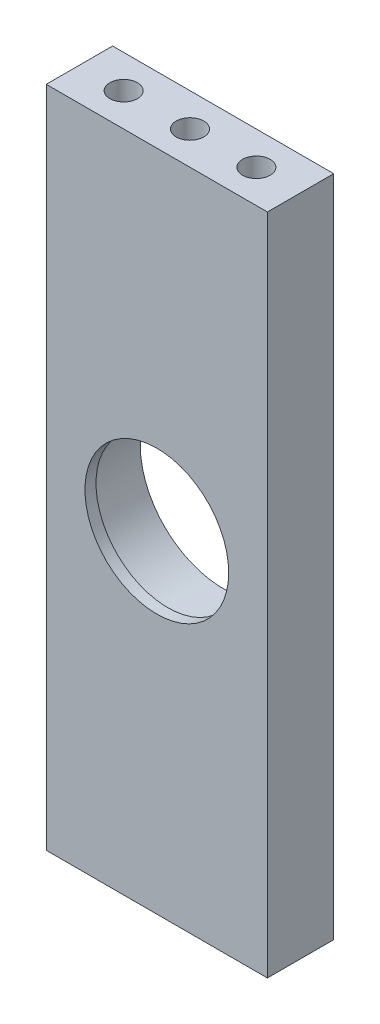
SolidWorks part; units mm, degrees
ref_plane "정면" through (0, 0, 0) normal (0, 0, 1) x (1, 0, 0)
ref_plane "윗면" through (0, 0, 0) normal (0, 1, 0) x (1, 0, 0)
ref_plane "우측면" through (0, 0, 0) normal (1, 0, 0) x (0, 0, -1)
sketch "스케치1" plane through (0, 0, 0) normal (0, 0, 1) x (1, 0, 0)
  line L2 (-7.7841, 20.7102) -> (-7.7841, -9.2898)
  line L3 (-7.7841, -9.2898) -> (12.2159, -9.2898)
  line L4 (12.2159, 20.7102) -> (12.2159, -9.2898)
  line L6 (-7.7841, 20.7102) -> (-7.7841, 50.7102)
  line L7 (-7.7841, 50.7102) -> (12.2159, 50.7102)
  line L8 (12.2159, 20.7102) -> (12.2159, 50.7102)
  circle A0 centre (2.2159, 20.7102) radius 7.5
  dimension "D3" = 15
  dimension "D1" = 20
  dimension "D2" = 30
extrude "보스-돌출1" add sketch "스케치1" along normal blind 6
sketch "스케치2" plane through (0, 0, 6) normal (0, 0, 1) x (1, 0, 0)
  circle A1 centre (2.2159, 20.7102) radius 6.5
  circle A2 centre (2.2159, 20.7102) radius 7.5
  circle A3 centre (2.2159, 20.7102) radius 7.5
  dimension "D1" = 0
  dimension "D2" = 1
extrude "보스-돌출3" add sketch "스케치2" against normal blind 1
sketch "스케치3" plane through (0, -9.2898, 0) normal (0, -1, 0) x (1, 0, 0)
  line L0 (-7.7841, 3) -> (49992.2159, 3) construction
  line L2 (-7.7841, 0) -> (12.2159, 0) construction
  line L3 (2.2159, 4) -> (2.2159, -49996) construction
  line L4 (-7.7841, 6) -> (12.2159, 6) construction
  circle A0 centre (2.2159, 3) radius 1.5
  circle A1 centre (-3.7841, 3) radius 1.5
  circle A2 centre (8.2159, 3) radius 1.5
  point P8 (2.2159, 6)
  dimension "D2" = 3
  dimension "D3" = 3
  dimension "D4" = 3
  dimension "D1" = 3
  dimension "D5" = 6
  dimension "D6" = 6
sketch "스케치4" plane through (0, 50.7102, 0) normal (0, 1, 0) x (1, 0, 0)
  line L0 (-7.7841, -3) -> (49992.2159, -3) construction
  line L1 (-7.7841, -6) -> (-7.7841, 0) construction
  line L2 (2.2159, -2) -> (2.2159, 49998) construction
  circle A0 centre (8.2159, -3) radius 1.5
  circle A1 centre (-3.7841, -3) radius 1.5
  circle A2 centre (2.2159, -3) radius 1.5
  point P4 (-7.7841, -3)
  dimension "D1" = 3
  dimension "D2" = 3
  dimension "D3" = 3
  dimension "D4" = 10
  dimension "D5" = 6
  dimension "D6" = 6
hole_wizard "M3 나사 구멍1" positions "스케치5" profile "스케치6" tap size "M3" standard "ISO"
sketch "스케치5" plane through (0, -9.2898, 0) normal (0, -1, 0) x (-1, 0, 0)
  point P0 (3.7841, -3)
  point P3 (-2.2159, -3)
  point P6 (-8.2159, -3)
sketch "스케치6" plane through (-3.7841, -9.2898, 3) normal (1, 0, 0) x (0, 0, -1)
  line L0 (0, 0) -> (0, 10.7511)
  line L1 (0, 10.7511) -> (1.25, 10)
  line L2 (1.25, 10) -> (1.25, 0)
  line L5 (1.25, 0) -> (0, 0)
  line L10 (0, 10.7511) -> (-1.25, 10) construction
  line L11 (0, -6.35) -> (0, 107.95) construction
  dimension "탭 드릴 지름" = 2.5
  dimension "탭 드릴 깊이" = 10
  dimension "드릴 각도" = 118
cosmetic thread "구멍 나사산1" parameters "D1"=6, "D2"=3
cosmetic thread "구멍 나사산2" parameters "D1"=6, "D2"=3
cosmetic thread "구멍 나사산3" parameters "D1"=6, "D2"=3
hole_wizard "M3 나사 구멍2" positions "스케치7" profile "스케치8" tap size "M3" standard "ISO"
sketch "스케치7" plane through (0, 50.7102, 0) normal (0, 1, 0) x (1, 0, 0)
  point P0 (-3.7841, -3)
  point P3 (2.2159, -3)
  point P6 (8.2159, -3)
sketch "스케치8" plane through (-3.7841, 50.7102, 3) normal (1, 0, 0) x (0, 0, 1)
  line L0 (0, 0) -> (0, 10.7511)
  line L1 (0, 10.7511) -> (1.25, 10)
  line L2 (1.25, 10) -> (1.25, 0)
  line L5 (1.25, 0) -> (0, 0)
  line L10 (0, 10.7511) -> (-1.25, 10) construction
  line L11 (0, -6.35) -> (0, 107.95) construction
  dimension "탭 드릴 지름" = 2.5
  dimension "탭 드릴 깊이" = 10
  dimension "드릴 각도" = 118
cosmetic thread "구멍 나사산4" parameters "D1"=6, "D2"=3
cosmetic thread "구멍 나사산5" parameters "D1"=6, "D2"=3
cosmetic thread "구멍 나사산6" parameters "D1"=6, "D2"=3
